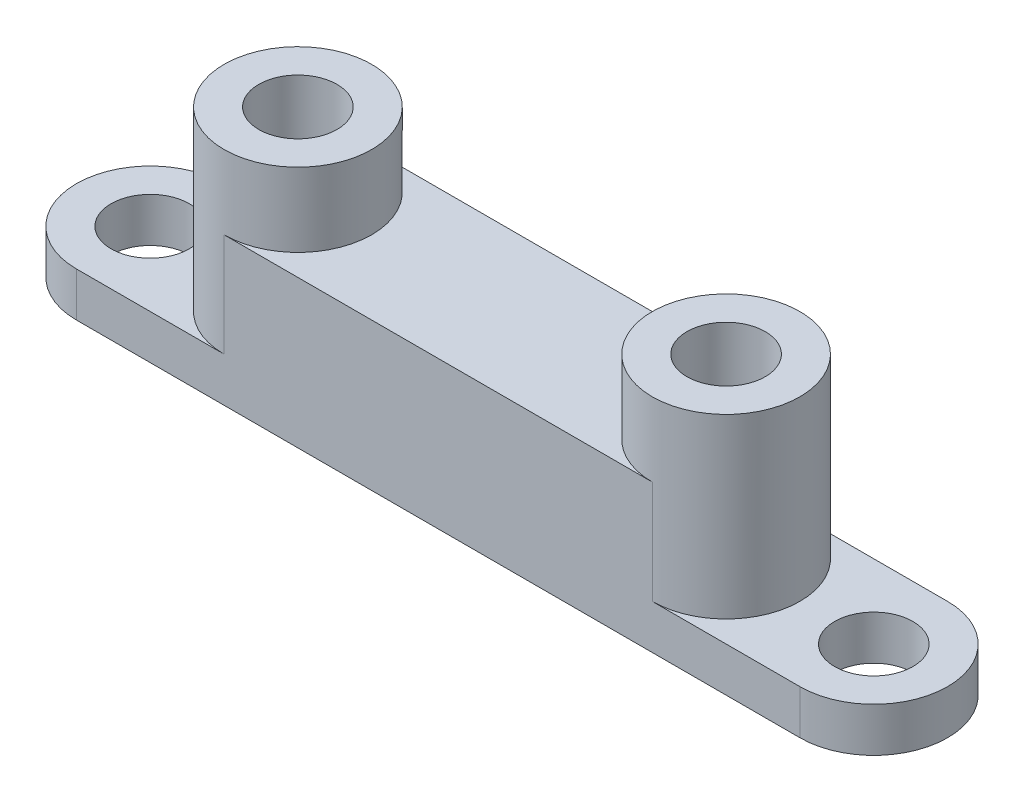
SolidWorks part; units mm, degrees
other "Marquage1"
sketch "Esquisse6" plane through (39, 15, 0) normal (0.0122, 0.9979, 0.0643) x (0.9817, -0.0242, 0.1888)
sketch "Esquisse9" plane through (49.0019, 15, 0) normal (0.0122, 0.9979, 0.0643) x (0.9817, -0.0242, 0.1888)
sketch "Esquisse15" plane through (49.0019, 26.5, 0) normal (0.0122, 0.9979, 0.0643) x (0.9817, -0.0242, 0.1888)
ref_plane "Plan de face" through (0, 0, 0) normal (0, 0, 1) x (1, 0, 0)
ref_plane "Plan de dessus" through (0, 0, 0) normal (0, 1, 0) x (1, 0, 0)
ref_plane "Plan de droite" through (0, 0, 0) normal (1, 0, 0) x (0, 0, -1)
sketch "Esquisse1" plane through (0, 0, 0) normal (0, 1, 0) x (1, 0, 0)
  line L0 (5, 5) -> (34, 5) construction
  line L1 (5, 0) -> (34, 0)
  line L3 (5, 10) -> (34, 10)
  line L5 (0, 10) -> (10, 0) construction
  circle A0 centre (5, 5) radius 2.65
  circle A1 centre (34, 5) radius 2.65
  arc A2 (5, 10) -> (5, 0) centre (5, 5) ccw
  arc A3 (34, 0) -> (34, 10) centre (34, 5) ccw
  point P12 (5, 5)
  dimension "D2" = 5.3
  dimension "D3" = 5.3
  dimension "D1" = 29
extrude "Boss.-Extru.1" add sketch "Esquisse1" along normal blind 15
sketch "Esquisse2" plane through (0, 0, 0) normal (0, -1, 0) x (1, 0, 0)
  circle A0 centre (5, -5) radius 3.4889
  circle A1 centre (34, -5) radius 3.5738
extrude "Boss.-Extru.2" add sketch "Esquisse2" against normal blind 4
sketch "Esquisse3" plane through (0, 15, 0) normal (0, 1, 0) x (1, 0, 0)
  line L0 (5, 10) -> (34, 10)
  line L1 (5, 0) -> (34, 0)
  arc A0 (5, 0) -> (5, 10) centre (5, 5) ccw
  arc A1 (34, 10) -> (34, 0) centre (34, 5) ccw
extrude "Enlèv. mat.-Extru.1" cut sketch "Esquisse3" against normal blind 5
sketch "Esquisse8" plane through (0, 0, 0) normal (0, -1, 0) x (1, 0, 0)
  line L0 (44.0019, -5) -> (-5.0019, -5) construction
  line L1 (44.0019, -10) -> (-5.0019, -10)
  line L2 (44.0019, 0) -> (-5.0019, 0)
  line L3 (5, 0) -> (34, 0) construction
  line L4 (34, -10) -> (5, -10) construction
  arc A0 (44.0019, -10) -> (44.0019, 0) centre (44.0019, -5) ccw
  arc A1 (-5.0019, 0) -> (-5.0019, -10) centre (-5.0019, -5) ccw
  circle A2 centre (-5.0019, -5) radius 2.65
  circle A3 centre (44.0019, -5) radius 2.65
  point P2 (19.5, -5)
  point P13 (19.5, 0)
  dimension "D1" = 5.3
  dimension "D2" = 5.3
extrude "Boss.-Extru.3" add sketch "Esquisse8" against normal blind 3
